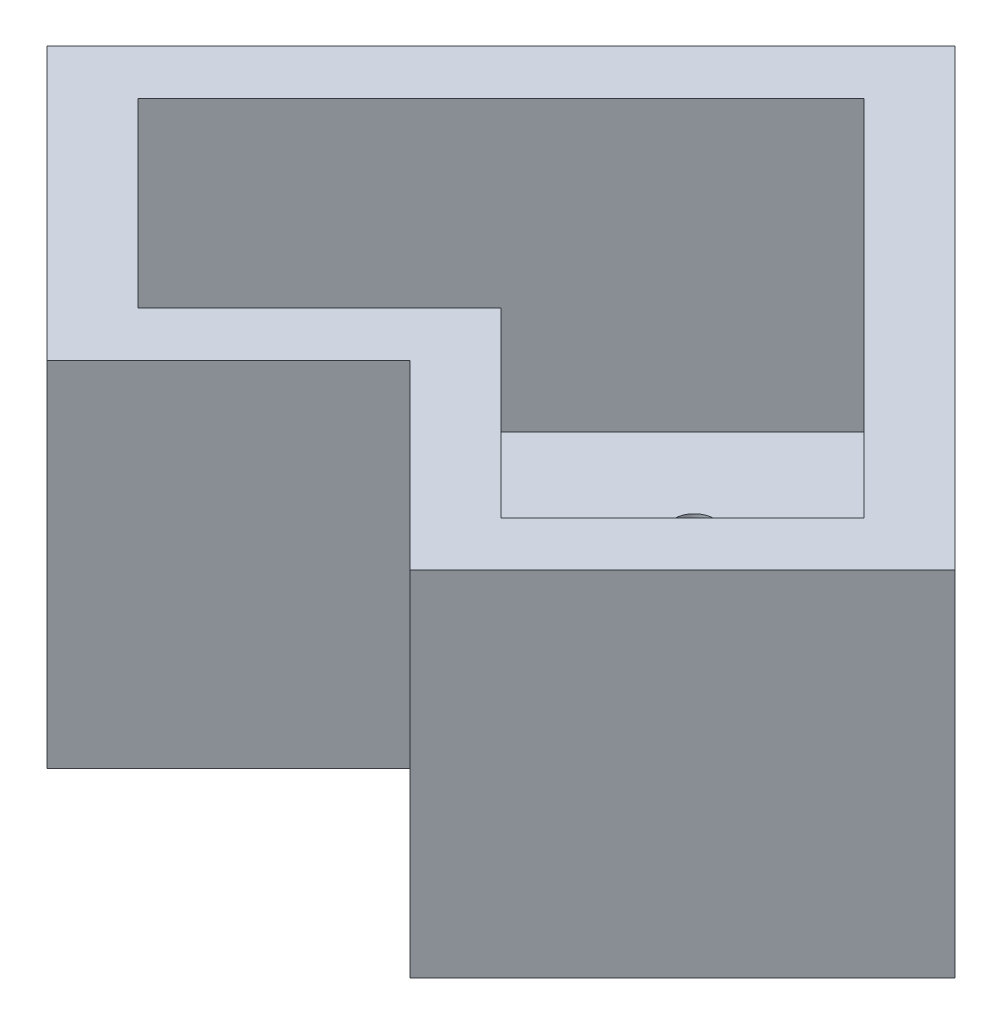
SolidWorks part; units mm, degrees
ref_plane "Front Plane" through (0, 0, 0) normal (0, 0, 1) x (1, 0, 0)
ref_plane "Top Plane" through (0, 0, 0) normal (0, 1, 0) x (1, 0, 0)
ref_plane "Right Plane" through (0, 0, 0) normal (1, 0, 0) x (0, 0, -1)
sketch "Sketch1" plane through (0, 0, 0) normal (0, 1, 0) x (1, 0, 0)
  line L0 (0, 0) -> (5.6569, -5.6569)
  line L2 (14.1421, 2.8284) -> (0, 16.9706)
  line L5 (-5.6569, -5.6569) -> (0, 0)
  line L6 (0, 16.9706) -> (-14.1421, 2.8284)
  line L7 (-14.1421, 2.8284) -> (-5.6569, -5.6569)
  line L8 (5.6569, -5.6569) -> (14.1421, 2.8284)
  point P3 (0, 8.4853)
  point P8 (-5.6569, 2.8284)
  point P9 (5.6569, 2.8284)
  dimension "D1" = 12
  dimension "D2" = 12
  dimension "D3" = 90
  dimension "D4" = 90
  dimension "D5" = 20
  dimension "D6" = 20
  dimension "D7" = 6
  dimension "D8" = 6
  dimension "D9" = 6
  dimension "D10" = 6
  dimension "D11" = 6
  dimension "D12" = 6
extrude "Boss-Extrude1" add sketch "Sketch1" along normal blind 11
shell "Shell1" thickness 2
sketch "Sketch2" plane through (0, 2, 0) normal (0, 1, 0) x (1, 0, 0)
  line L0 (-14.1421, 2.8284) -> (-5.6569, -5.6569) construction
  line L1 (-5.6569, -5.6569) -> (0, 0) construction
  line L3 (14.1421, 2.8284) -> (0, 16.9706) construction
  line L4 (5.6569, -5.6569) -> (14.1421, 2.8284) construction
  circle A1 centre (5.6569, 2.8284) radius 3
  circle A2 centre (-5.6569, 2.8284) radius 3
  circle A3 centre (0, 7.5784) radius 3
  point P0 (5.6569, 2.8284)
  point P1 (0, 7.5784)
  point P2 (-5.6569, 2.8284)
  point P17 (0, 0)
  point P20 (0, 0)
  point P24 (0, 0)
  dimension "D7" = 6
  dimension "D8" = 6
  dimension "D3" = 6
  dimension "D1" = 6
  dimension "D2" = 6
  dimension "D4" = 4.75
  dimension "D5" = 6
  dimension "D6" = 6
sketch "Sketch3" plane through (0, 0, 0) normal (0, -1, 0) x (1, 0, 0)
  circle A0 centre (-5.6569, -1.5584) radius 0.625
  circle A1 centre (-5.6569, -4.0984) radius 0.625
  circle A2 centre (0, -6.3084) radius 0.625
  circle A3 centre (0, -8.8484) radius 0.625
  circle A4 centre (5.6569, -1.5584) radius 0.625
  circle A5 centre (5.6569, -4.0984) radius 0.625
  point P0 (-5.6569, -1.5584)
  point P1 (-5.6569, -4.0984)
  point P2 (0, -6.3084)
  point P3 (0, -8.8484)
  point P4 (5.6569, -4.0984)
  point P5 (5.6569, -1.5584)
  dimension "D1" = 1.25
  dimension "D2" = 1.25
  dimension "D3" = 1.25
  dimension "D4" = 1.25
  dimension "D5" = 1.25
  dimension "D6" = 1.25
extrude "Cut-Extrude1" cut sketch "Sketch3" against normal blind 10
